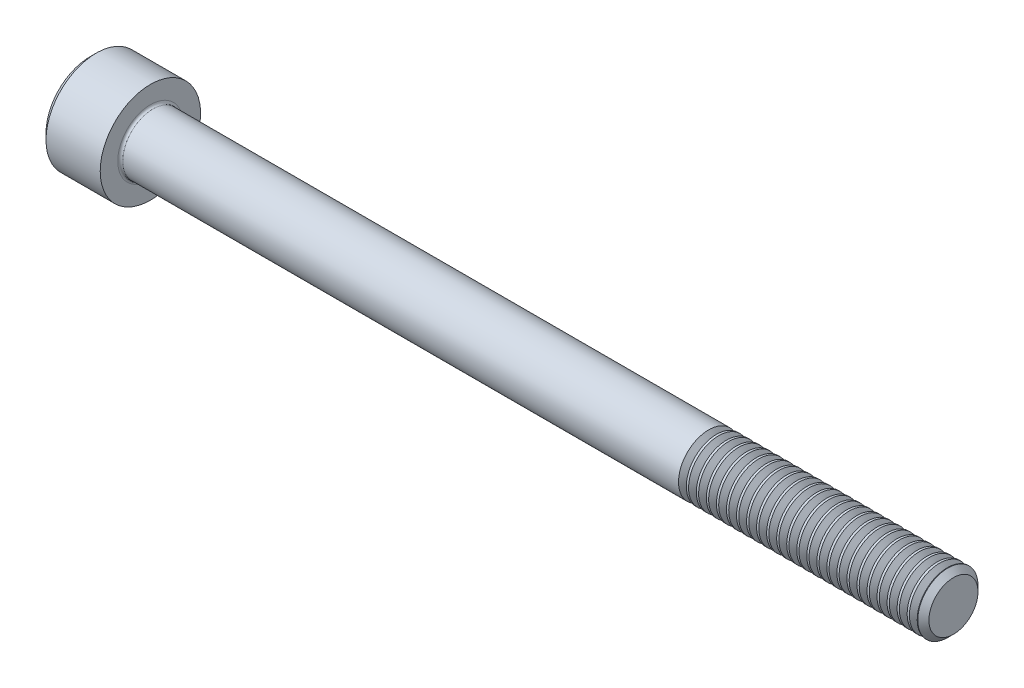
SolidWorks part; units mm, degrees
revolve "Base-Revolve" add sketch "BodySke"
sketch "BodySke" plane through (0, 0, 0) normal (0, 0, 1) x (1, 0, 0)
  line L0 (0, 0) -> (0, 4.4)
  line L1 (0.6, 5) -> (6, 5)
  line L2 (6, 5) -> (6, 3)
  line L3 (6, 3) -> (85.4455, 3)
  line L4 (86, 2.4455) -> (86, 0)
  line L5 (86, 0) -> (0, 0)
  line L6 (-31.75, 0) -> (127, 0) construction
  line L7 (0, 4.4) -> (0.6, 5)
  line L8 (86, 2.4455) -> (85.4455, 3)
  line L9 (0, -4.4) -> (0.6, -5) construction
  line L10 (86, -2.4455) -> (85.4455, -3) construction
  line L11 (7, 9.525) -> (7, 3.175) construction
  line L12 (62, 9.525) -> (62, 3.175) construction
  line L13 (36, 9.525) -> (36, 3.175) construction
  dimension "Diameter" = 6
  dimension "Head_ht" = 6
  dimension "Length" = 80
  dimension "Body_ch_ang" = 45
  dimension "Head_dia" = 10
  dimension "Head_ch_ang" = 45
  dimension "Minor_dia" = 4.891
  dimension "Advance" = 1
  dimension "Thread_nom" = 24
  dimension "Thread_length" = 50
  dimension "Head_ch_ht" = 0.6
cosmetic thread "ThreadCosmetic" [suppressed]
fillet "Fillet1" radius 0.25 1 edges at (6, 0, 3)
ref_plane "Plane1" through (0, 0, 0) normal (0, 0, 1) x (1, 0, 0)
ref_plane "Plane2" through (0, 0, 0) normal (0, 1, 0) x (1, 0, 0)
ref_plane "Plane3" through (0, 0, 0) normal (1, 0, 0) x (0, 0, -1)
sketch "Sketch2" plane through (0, 0, 0) normal (0, 0, 1) x (1, 0, 0)
  line L0 (0, 2.542) -> (3, 2.542)
  line L1 (3, 2.542) -> (4.4676, 0)
  line L2 (-31.75, 0) -> (127, 0) construction
  line L3 (4.4676, 0) -> (0, 0)
  line L4 (0, 0) -> (0, 2.542)
  line L5 (0, 4.4) -> (0, -4.4) construction
  line L6 (0, 0) -> (47.625, 0) construction
  line L7 (6, -5) -> (6, 5) construction
  dimension "D2" = 60
revolve "Hex-PreBroach" cut sketch "Sketch2" angle 360 about L6
sketch "Sketch3" plane through (0, 0, 0) normal (-1, 0, 0) x (0, 0.5, 0.866)
  line L0 (1.4676, 2.542) -> (-1.4676, 2.542)
  line L1 (-1.4676, 2.542) -> (-2.9352, 0)
  line L2 (1.4676, 2.542) -> (2.9352, 0)
  line L3 (1.4676, -2.542) -> (2.9352, 0)
  line L4 (1.4676, -2.542) -> (-1.4676, -2.542)
  line L5 (-1.4676, -2.542) -> (-2.9352, 0)
extrude "Hex" cut sketch "Sketch3" against normal blind 3
sketch "Sketch4" plane through (0, 0, 0) normal (-1, 0, 0) x (0, 0, 1)
  line L0 (0, 0) -> (2.8067, 0)
  line L1 (0, 0) -> (6.1484, 3.5498) construction
  line L2 (0, 0) -> (1.4033, 2.4307)
  line L3 (2.3336, 0.614) -> (2.6851, 0.817)
  line L4 (1.6986, 1.7139) -> (2.0501, 1.9169)
  arc A0 (2.3336, 0.614) -> (1.6986, 1.7139) centre (0, 0) ccw
  arc A1 (2.8067, 0) -> (2.6851, 0.817) centre (0, 0) ccw
  arc A2 (1.4033, 2.4307) -> (2.0501, 1.9169) centre (0, 0) cw
  dimension "D1" = 30
  dimension "D2" = 60
extrude "Spline" [suppressed] cut sketch "Sketch4" against normal blind 3
pattern_circular "CirPattern1" [suppressed] count 6 every 60
sketch "Sketch5" plane through (0, 0, 0) normal (0, 0, 1) x (1, 0, 0)
  line L0 (-31.75, 0) -> (127, 0) construction
  line L2 (0, 4.4) -> (0, -4.4) construction
  circle A0 centre (2.3, 0) radius 0.675
  dimension "Drilled_hole_dia" = 1.35
  dimension "Drilled_hole_loc" = 2.3
extrude "Hole" [suppressed] cut sketch "Sketch5" against normal through all and the other way through all
pattern_circular "Drilled-4" [suppressed] count 2 every 60
pattern_circular "Drilled-6" [suppressed] count 3 every 60
sketch "ThdSchSke" plane through (0, 0, 0) normal (0, 0, 1) x (1, 0, 0)
  line L0 (62, -2.4455) -> (61.6117, -3)
  line L1 (62, -2.4455) -> (62.3883, -3)
  line L2 (62.3883, -3) -> (62.3883, -3.75)
  line L3 (-3.175, 0) -> (5.1513, 0) construction
  line L5 (62.3883, -3.75) -> (61.6117, -3.75)
  line L6 (61.6117, -3.75) -> (61.6117, -3)
  line L7 (0, 4.4) -> (0, -4.4) construction
revolve "ThreadSchematic" cut sketch "ThdSchSke" angle 360 about L3
pattern_linear "ThdSchPat" count 24 spacing 1 along (1, 0, 0) of "ThreadSchematic"
equation "\"D2@Sketch3\" = \"Hex_size@Sketch3\" / 2"
equation "\"D1@Sketch3\" = \"Hex_size@Sketch3\" / 2"
equation "\"D1@Sketch2\" = \"Hex_size@Sketch3\" / 2"
equation "\"D3@Sketch4\" = \"Spline_p_dim@Sketch4\" / 2"
equation "\"Thread_minor@ThreadCosmetic\"  =  \"Minor_dia@BodySke\""
equation "\"D2@CirPattern1\" = 360 / \"Num_teeth@CirPattern1\""
equation "\"Wall_thickness@Sketch2\" = \"Head_ht@BodySke\" - \"Key_eng@Hex\""
equation "\"Thread_length@ThreadCosmetic\" = ((sgn( (\"Length@BodySke\" - \"Advance@BodySke\" ) - \"Thread_nom@BodySke\" )-1)*( (\"Length@BodySke\" - \"Advance@BodySke\" ) - \"Thread_nom@BodySke\" ))/-2+ \"Thread_nom@BodySke\""
equation "\"Thread_minor@ThdSchSke\" = \"Minor_dia@BodySke\""
equation "\"Diameter@ThdSchSke\" = \"Diameter@BodySke\""
equation "\"Overcut@ThdSchSke\" = \"Diameter@BodySke\" * 1.25"
equation "\"Start@ThdSchSke\" = \"Head_ht@BodySke\" + \"Length@BodySke\" - \"Thread_length@ThreadCosmetic\"  '---Non-countersunk---"
equation "\"Num_threads@ThdSchPat\" = int( \"Thread_length@ThreadCosmetic\" / \"Advance@BodySke\" + 0.999 )  + 1"
equation "\"Advance@ThdSchPat\" = \"Thread_length@ThreadCosmetic\" /  (\"Num_threads@ThdSchPat\" - 1) 'relax it"
equation "\"Num_threads@ThdSchPat\" = \"Num_threads@ThdSchPat\" - sgn( \"Num_threads@ThdSchPat\" - 1) '---chamfered tips only---"
